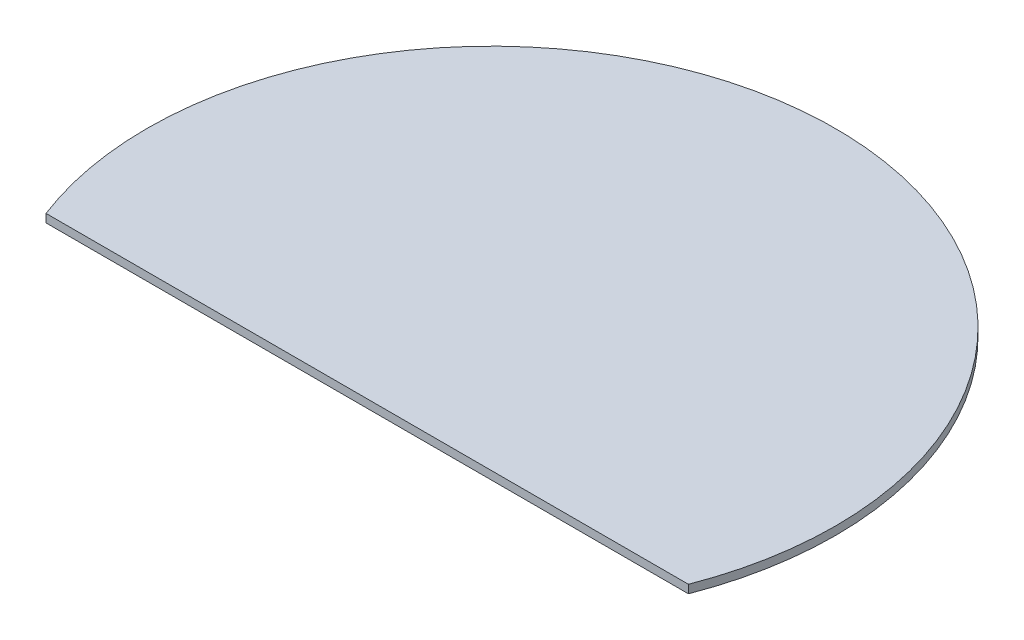
SolidWorks part; units mm, degrees
ref_plane "Front Plane" through (0, 0, 0) normal (0, 0, 1) x (1, 0, 0)
ref_plane "Top Plane" through (0, 0, 0) normal (0, 1, 0) x (1, 0, 0)
ref_plane "Right Plane" through (0, 0, 0) normal (1, 0, 0) x (0, 0, -1)
sketch "Sketch2" plane through (0, 0, 0) normal (0, 1, 0) x (1, 0, 0)
  circle A0 centre (-17.8077, -0.8549) radius 125
  dimension "D1" = 250
extrude "Boss-Extrude1" add sketch "Sketch2" along normal blind 3
sketch "Sketch3" plane through (0, 0, 0) normal (0, -1, 0) x (1, 0, 0)
  line L0 (-134.4267, 45.8549) -> (98.8114, 45.8549)
  circle A0 centre (-17.8077, 0.8549) radius 125 construction
  circle A1 centre (-17.8077, 0.8549) radius 125
  circle M2 centre (-17.8077, 0.8549) radius 125
  dimension "D1" = 45
extrude "Cut-Extrude1" cut sketch "Sketch3" against normal blind 3 contours L0 M2
